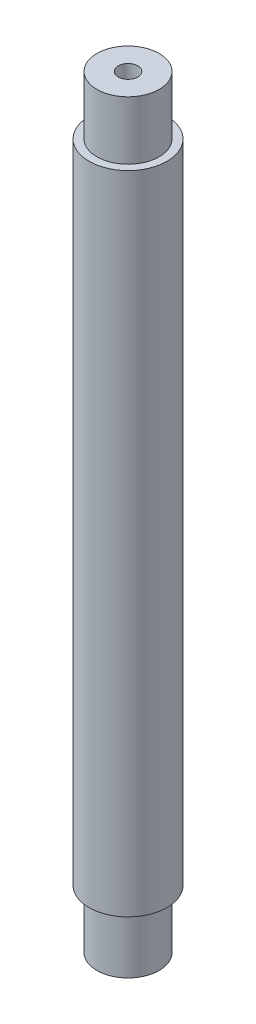
SolidWorks part; units mm, degrees
ref_plane "Płaszczyzna przednia" through (0, 0, 0) normal (0, 0, 1) x (1, 0, 0)
ref_plane "Płaszczyzna górna" through (0, 0, 0) normal (0, 1, 0) x (1, 0, 0)
ref_plane "Płaszczyzna prawa" through (0, 0, 0) normal (1, 0, 0) x (0, 0, -1)
sketch "Szkic1" plane through (0, 0, 0) normal (0, 0, 1) x (1, 0, 0)
  line L0 (0, 0) -> (0, 196)
  line L1 (0, 0) -> (8, 0)
  line L2 (8, 0) -> (8, 15)
  line L3 (8, 15) -> (10, 15)
  line L4 (10, 15) -> (10, 181)
  line L5 (10, 181) -> (8, 181)
  line L6 (8, 181) -> (8, 196)
  line L7 (8, 196) -> (0, 196)
  line L8 (2.5, 196) -> (2.5, 178)
  line L9 (2.5, 178) -> (8, 178)
  line L10 (8, 178) -> (8, 18)
  line L11 (8, 18) -> (0, 18)
  dimension "D1" = 160
  dimension "D2" = 10
  dimension "D3" = 8
  dimension "D4" = 8
  dimension "D5" = 15
  dimension "D6" = 15
  dimension "D7" = 3
  dimension "D8" = 2.5
  dimension "D9" = 3
revolve "Obrót1" add sketch "Szkic1" angle 360 about L0
